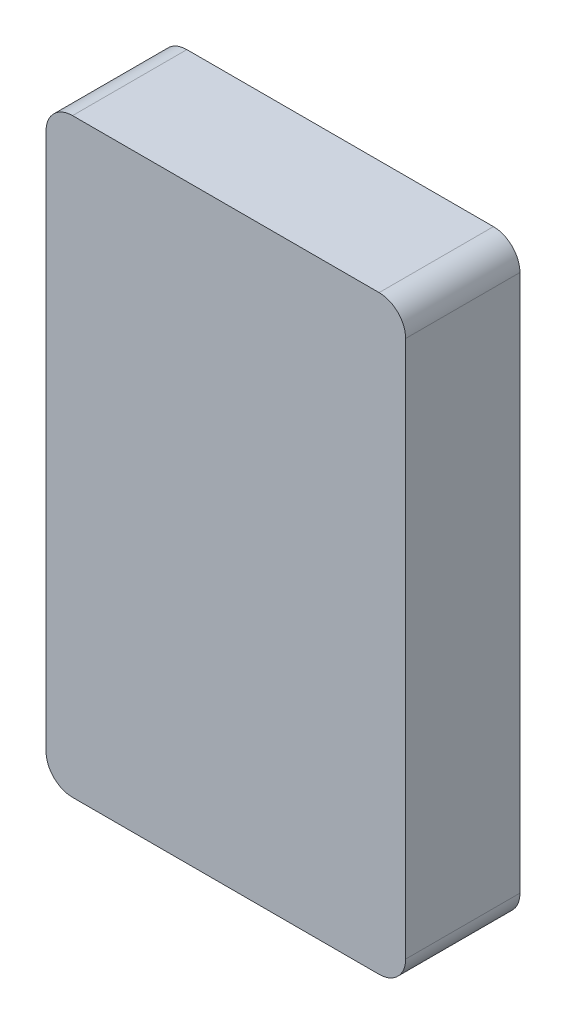
SolidWorks part; units mm, degrees
ref_plane "Front Plane" through (0, 0, 0) normal (0, 0, 1) x (1, 0, 0)
ref_plane "Top Plane" through (0, 0, 0) normal (0, 1, 0) x (1, 0, 0)
ref_plane "Right Plane" through (0, 0, 0) normal (1, 0, 0) x (0, 0, -1)
sketch "Sketch1" plane through (0, 0, 0) normal (0, 0, 1) x (1, 0, 0)
  line L0 (-197.5, 700) -> (-197.5, 740) construction
  line L1 (0, 0) -> (-395, 0)
  line L2 (0, 0) -> (0, 700)
  line L3 (0, 700) -> (-395, 700)
  line L4 (-395, 0) -> (-395, 700)
  line L5 (-400, 740) -> (5, 740)
  line L6 (-435, 705) -> (-435, -5)
  line L7 (-400, -40) -> (5, -40)
  line L8 (40, 705) -> (40, -5)
  arc A0 (5, -40) -> (40, -5) centre (5, -5) ccw
  arc A1 (5, 740) -> (40, 705) centre (5, 705) cw
  arc A2 (-400, 740) -> (-435, 705) centre (-400, 705) ccw
  arc A3 (-435, -5) -> (-400, -40) centre (-400, -5) ccw
  dimension "D5" = 35
  dimension "D4" = 35
  dimension "D1" = 395
  dimension "D2" = 700
  dimension "D3" = 40
  dimension "D6" = 40
  dimension "D7" = 40
extrude "Boss-Extrude1" add sketch "Sketch1" along normal blind 150
sketch "Sketch2" plane through (0, 0, 150) normal (0, 0, 1) x (1, 0, 0)
  line L0 (-400, -40) -> (5, -40) construction
  line L1 (-435, 705) -> (-435, -5) construction
  line L2 (5, 740) -> (-400, 740) construction
  line L3 (40, -5) -> (40, 705) construction
  line L4 (-400, -40) -> (5, -40)
  line L5 (-435, 705) -> (-435, -5)
  line L6 (5, 740) -> (-400, 740)
  line L7 (40, -5) -> (40, 705)
  arc A0 (5, -40) -> (40, -5) centre (5, -5) ccw construction
  arc A1 (-435, -5) -> (-400, -40) centre (-400, -5) ccw construction
  arc A2 (-400, 740) -> (-435, 705) centre (-400, 705) ccw construction
  arc A3 (40, 705) -> (5, 740) centre (5, 705) ccw construction
  arc A4 (5, -40) -> (40, -5) centre (5, -5) ccw
  arc A5 (-435, -5) -> (-400, -40) centre (-400, -5) ccw
  arc A6 (-400, 740) -> (-435, 705) centre (-400, 705) ccw
  arc A7 (40, 705) -> (5, 740) centre (5, 705) ccw
extrude "Boss-Extrude2" add sketch "Sketch2" along normal blind 1
